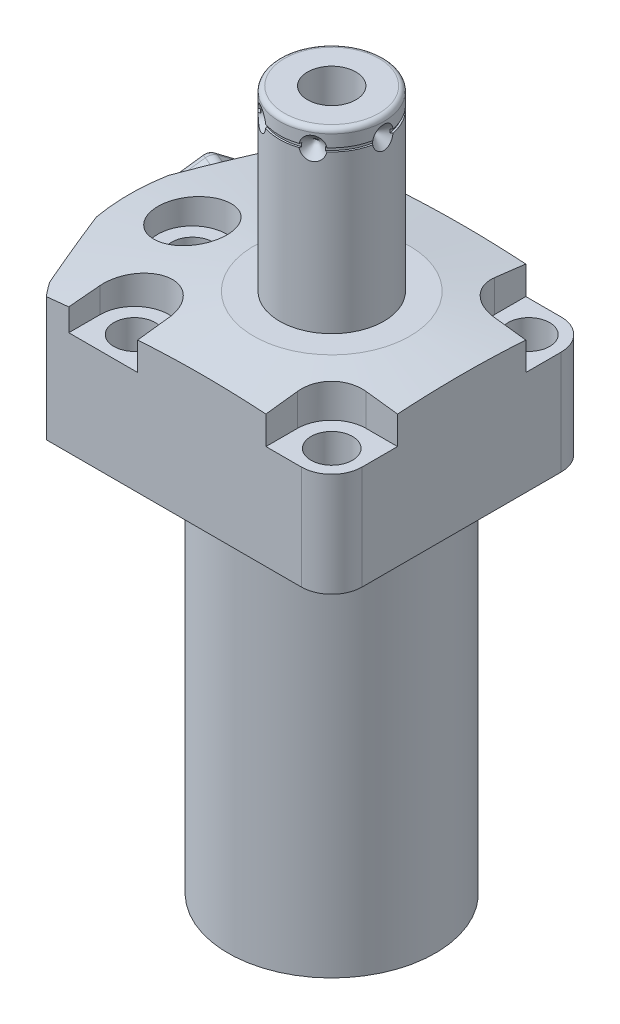
SolidWorks part; units mm, degrees
material "Alloy Steel"
ref_plane "Front Plane" through (0, 0, 0) normal (0, 0, 1) x (1, 0, 0)
ref_plane "Top Plane" through (0, 0, 0) normal (0, 1, 0) x (1, 0, 0)
ref_plane "Right Plane" through (0, 0, 0) normal (1, 0, 0) x (0, 0, -1)
sketch "S2D0002" plane through (0, 0, 0) normal (0, 0, 1) x (1, 0, 0)
  line L0 (-43.18, 0) -> (-43.18, 30.1498)
  line L1 (-43.18, 30.1498) -> (0, 30.1498)
  line L2 (0, 30.1498) -> (0, -80.9752)
  line L3 (0, -80.9752) -> (-22.098, -80.9752)
  line L4 (-22.098, -80.9752) -> (-22.098, 0)
  line L5 (-22.098, 0) -> (-43.18, 0)
  line L6 (0, -3.4925) -> (0, 73.3425) construction
  dimension "D1" = 111.125
  dimension "D2" = 44.196
  dimension "D3" = 86.36
  dimension "D4" = 80.9752
revolve "Revolve1" add sketch "S2D0002" angle 360 about L6
sketch "S2D0001" plane through (0, 0, 0) normal (0, -1, 0) x (1, 0, 0)
  line L0 (-33.136, -27.686) -> (33.136, -27.686)
  line L2 (33.136, 27.686) -> (-33.136, 27.686)
  line L3 (0, 0) -> (59.5614, 0) construction
  arc A0 (-33.136, -27.686) -> (33.136, -27.686) centre (0, 0) ccw
  circle A1 centre (0, 0) radius 43.18
  arc A2 (33.136, 27.686) -> (-33.136, 27.686) centre (0, 0) ccw
  point P4 (25.1041, 0)
  dimension "D1" = 55.372
  dimension "D2" = 0
extrude "Cut-Extrude1" cut sketch "S2D0001" against normal blind 32.9946
sketch "Sketch3" plane through (0, 30.1498, 0) normal (0, -1, 0) x (-1, 0, 0)
  line L0 (21.3317, 58.747) -> (45.6655, 0)
  line L1 (45.6655, 0) -> (21.3317, -58.747)
  line L2 (-32.7616, -13.5703) -> (61.25, 25.3706) construction
  line L3 (0, 0) -> (47.9453, 0) construction
  arc A0 (21.3317, -58.747) -> (21.3317, 58.747) centre (0, 0) ccw
  dimension "D3" = 125
  dimension "D1" = 22.5
  dimension "D2" = 42.1894
extrude "Cut-Extrude2" cut sketch "Sketch3" along normal up to surface (30.1498 mm away) up to face at (0, 0, -22.098)
sketch "Sketch4" plane through (0, 0, 0) normal (0, -1, 0) x (1, 0, 0)
  line L0 (27.686, -33.136) -> (27.686, 33.136)
  line L1 (-33.136, 27.686) -> (33.136, 27.686) construction
  arc A0 (27.686, -33.136) -> (27.686, 33.136) centre (0, 0) ccw
  arc A1 (33.136, -27.686) -> (33.136, 27.686) centre (0, 0) ccw construction
  dimension "D1" = 27.686
extrude "Cut-Extrude3" cut sketch "Sketch4" against normal blind 32.9946
fillet "Fillet1" radius 6.477 2 edges at (27.686, 15.0749, 27.686) (27.686, 15.0749, -27.686)
sketch "Sketch5" plane through (0, 30.1498, 0) normal (0, 1, 0) x (-1, 0, 0)
  line L0 (0, 0) -> (-37.3124, 0) construction
  line L1 (-27.686, 21.209) -> (-27.686, -21.209) construction
  line L2 (-21.209, -27.686) -> (33.136, -27.686) construction
  line L3 (-27.686, -13.6652) -> (-27.686, -27.686)
  line L4 (-27.686, -27.686) -> (-13.6652, -27.686)
  line L5 (-27.686, -13.6652) -> (-21.0058, -13.6652)
  line L6 (-13.6652, -21.0058) -> (-13.6652, -27.686)
  line L7 (-13.6652, 21.0058) -> (-13.6652, 27.686)
  line L8 (-27.686, 13.6652) -> (-21.0058, 13.6652)
  line L9 (0, 0.7832) -> (0, 0) construction
  line L10 (0, 0) -> (47.8281, 0) construction
  line L11 (-27.686, 27.686) -> (-13.6652, 27.686)
  line L12 (-27.686, 13.6652) -> (-27.686, 27.686)
  line L13 (0, 0) -> (0, 43.3168) construction
  line L14 (33.136, 27.686) -> (-21.209, 27.686) construction
  line L15 (13.6652, 27.686) -> (28.3464, 27.686)
  line L16 (13.6652, 27.686) -> (13.6652, 21.0058)
  line L17 (13.6652, -27.686) -> (13.6652, -21.0058)
  line L18 (28.3464, 27.686) -> (28.3464, 21.0058)
  line L19 (28.3464, -27.686) -> (28.3464, -21.0058)
  line L20 (13.6652, -27.686) -> (28.3464, -27.686)
  arc A0 (-13.6652, -21.0058) -> (-21.0058, -13.6652) centre (-21.0058, -21.0058) ccw
  arc A1 (-13.6652, 21.0058) -> (-21.0058, 13.6652) centre (-21.0058, 21.0058) cw
  arc A2 (28.3464, 21.0058) -> (13.6652, 21.0058) centre (21.0058, 21.0058) cw
  arc A3 (28.3464, -21.0058) -> (13.6652, -21.0058) centre (21.0058, -21.0058) ccw
  dimension "D3" = 21.0058
  dimension "D1" = 7.3406
  dimension "D2" = 21.0058
  dimension "D4" = 21.0058
extrude "Cut-Extrude4" cut sketch "Sketch5" against normal blind 8.001
sketch "S2D0003" plane through (0, 0, 0) normal (0, 0, 1) x (1, 0, 0)
  line L0 (-16.637, 30.1498) -> (-86.637, 20.3119)
  line L1 (0, 12.958) -> (0, 26.6311) construction
  line L2 (-16.637, 30.1498) -> (-86.637, 30.1498)
  line L3 (-86.637, 30.1498) -> (-86.637, 20.3119)
  line L4 (-33.136, 30.1498) -> (-28.3464, 30.1498) construction
  dimension "D1" = 33.274
  dimension "D2" = 8
  dimension "D3" = 70
revolve "Cut-Revolve1" cut sketch "S2D0003" angle 360 about L1
ref_plane "Plane20" through (0, 14.5034, 0) normal (0, -1, 0) x (1, 0, 0)
sketch "Sketch7" plane through (0, 14.5034, 0) normal (0, -1, 0) x (1, 0, 0)
  line L0 (-41.1733, -10.1813) -> (-42.8571, -6.1163)
  line L1 (-41.1733, -10.1813) -> (-41.0456, -10.1577)
  line L2 (-41.0456, -10.1577) -> (-40.5499, -10.363)
  line L3 (-40.5499, -10.363) -> (-27.9234, -5.133)
  line L4 (-27.9234, -5.133) -> (-25.6489, -10.6241)
  line L5 (-25.6489, -10.6241) -> (-38.9779, -16.1452)
  line L6 (0, 0) -> (22.0051, 9.1148) construction
  line L7 (-42.4971, -7.6492) -> (-35.4588, -24.6412) construction
  line L8 (-42.8571, -6.1163) -> (-43.0918, -6.2135)
  line L9 (-43.0918, -6.2135) -> (-38.9779, -16.1452)
  line L11 (-42.4971, -7.6492) -> (-35.4588, -24.6412) construction
  dimension "D1" = 14.1732
  dimension "D2" = 11.8872
  dimension "D3" = 45
  dimension "D4" = 0.254
  dimension "D5" = 0.5064
  dimension "D6" = 12.7
  dimension "D7" = 21.5
  dimension "D8" = 78
revolve "Cut-Revolve2" cut sketch "Sketch7" angle 360 about L6
ref_plane "Plane21" through (0, 0, -11.8364) normal (0, 0, 1) x (1, 0, 0)
sketch "Sketch9" plane through (0, 0, -11.8364) normal (0, 0, 1) x (1, 0, 0)
  line L0 (-31.8262, 1.5) -> (-33.575, 1.5)
  line L1 (-31.8262, 1.5) -> (-31.8262, 4.4972)
  line L2 (-31.8262, 4.4972) -> (-29.8196, 4.4972)
  line L3 (-29.8196, 4.4972) -> (-29.8196, 12.0664)
  line L4 (-29.8196, 12.0664) -> (-28.575, 12.0664)
  line L5 (-28.575, 12.0664) -> (-28.575, 0)
  line L6 (-28.575, -17.8934) -> (-28.575, 0.5283) construction
  line L7 (-33.136, 0) -> (21.209, 0) construction
  line L8 (-33.575, 0) -> (-33.575, 1.5)
  line L9 (-35.4588, 0) -> (-42.4971, 0) construction
  line L10 (-33.575, 0) -> (-28.575, 0)
  dimension "D1" = 7.5692
  dimension "D2" = 2.9972
  dimension "D3" = 28.575
  dimension "D4" = 2.4892
  dimension "D5" = 6.5024
  dimension "D6" = 10
  dimension "D7" = 1.5
revolve "Cut-Revolve4" cut sketch "Sketch9" angle 360 about L6
sketch "Sketch11" plane through (0, 4.4972, 0) normal (0, -1, 0) x (1, 0, 0)
  circle A0 centre (-28.575, -11.8364) radius 2.7432
  circle A1 centre (-28.575, -11.8364) radius 3.2512 construction
  dimension "D1" = 5.4864
extrude "Extrude1" add sketch "Sketch11" along normal blind 2.9972
sketch "Sketch12" plane through (0, 1.5, 0) normal (0, -1, 0) x (1, 0, 0)
  line L7 (-27.3304, -12.555) -> (-27.3304, -11.1178)
  line L8 (-27.3304, -11.1178) -> (-28.575, -10.3993)
  line L9 (-28.575, -10.3993) -> (-29.8196, -11.1178)
  line L10 (-29.8196, -11.1178) -> (-29.8196, -12.555)
  line L11 (-29.8196, -12.555) -> (-28.575, -13.2735)
  line L12 (-28.575, -13.2735) -> (-27.3304, -12.555)
  circle A0 centre (-28.575, -11.8364) radius 1.2446 construction
  circle A1 centre (-28.575, -11.8364) radius 2.7432 construction
  dimension "D2" = 2.4892
extrude "Cut-Extrude5" cut sketch "Sketch12" against normal blind 1.27
chamfer "Chamfer1" distance 0.254 angle 45 1 edges at (-28.575, 1.5, -14.5796)
mirror "Mirror2" about plane through (0, 0, 0) normal (0, 0, 1) of "Chamfer1", "Cut-Extrude5", "Extrude1", "Cut-Revolve4", "Cut-Revolve2"
sketch "Sketch16" plane through (-18.1864, 0, -11.8364) normal (0, 0, -1) x (-1, 0, 0)
  line L0 (10.3886, -0.4101) -> (10.3886, 1.5457) construction
  line L1 (5.3886, 1.5) -> (15.3886, 1.5) construction
  line L2 (7.1374, 4.4972) -> (7.1374, 1.5) construction
  line L3 (13.6398, 1.5) -> (13.6398, 4.4972) construction
  circle A0 centre (14.3886, 0.5) radius 1
  dimension "D2" = 2
  dimension "D1" = 8
  dimension "D3" = 1
revolve "Revolve3" add sketch "Sketch16" angle 360 about L0
mirror "Mirror3" about plane through (0, 0, 0) normal (0, 0, 1) of bodies 123 141
sketch "Sketch17" plane through (0, 0, 0) normal (1, 0, 0) x (0, 0, -1)
  line L0 (0, 30.1498) -> (-11.1125, 30.1498)
  line L1 (-11.1125, 30.1498) -> (-11.1125, 67.018)
  line L2 (-10.0965, 68.034) -> (0, 68.034)
  line L3 (0, 68.034) -> (0, 30.1498)
  line L4 (0, 24.9961) -> (0, 47.2925) construction
  line L5 (16.637, 30.1498) -> (-16.637, 30.1498) construction
  line L6 (-24.6412, 0) -> (-7.6492, 0) construction
  arc A0 (-10.0965, 68.034) -> (-11.1125, 67.018) centre (-10.0965, 67.018) ccw
  dimension "D2" = 1.016
  dimension "D1" = 22.225
  dimension "D3" = 68.034
revolve "Revolve4" add sketch "Sketch17" angle 360 about L4
sketch "Sketch18" plane through (0, 0, 0) normal (0, 0, 1) x (1, 0, 0)
  line L0 (5.1562, 68.034) -> (5.1562, 51.016)
  line L1 (5.1562, 51.016) -> (0, 47.9178)
  line L2 (5.1562, 68.034) -> (0, 68.034)
  line L3 (0, 68.034) -> (0, 47.9178)
  line L4 (0, -20.476) -> (0, 0.5839) construction
  line L5 (10.0965, 68.034) -> (-10.0965, 68.034) construction
  dimension "D1" = 17.018
  dimension "D2" = 10.3124
  dimension "D3" = 59
revolve "Cut-Revolve7" cut sketch "Sketch18" angle 360 about L4
sketch "Sketch19" plane through (-52.2568, 0, 16.5766) normal (-0.9239, 0, -0.3827) x (-0.3827, 0, 0.9239)
  circle A0 centre (-35.3126, 14.5034) radius 8.5
  circle A1 centre (-35.3126, 14.5034) radius 5.9436 construction
  dimension "D1" = 17
extrude "Extrude3" add sketch "Sketch19" along normal blind 1
sketch "Sketch20" plane through (0, 0, 0) normal (0, 0, 1) x (1, 0, 0)
  line L3 (0, 64.0716) -> (4.3349, 64.0716) construction
  line L4 (-11.1125, 67.018) -> (-11.1125, 30.1498) construction
  line L5 (10.0965, 68.034) -> (-10.0965, 68.034) construction
  line L6 (-11.1125, 61.6586) -> (-11.1125, 64.0716)
  line L7 (-11.1125, 64.0716) -> (-8.6995, 64.0716)
  line L8 (-8.6995, 64.0716) -> (-11.1125, 61.6586)
  dimension "D1" = 3.9624
  dimension "D2" = 4.826
  dimension "D4" = 45
revolve "Cut-Revolve8" cut sketch "Sketch20" angle 360 about L3
sketch "Sketch22" plane through (0, 0, 0) normal (1, 0, 0) x (0, 0, -1)
  line L0 (11.1125, 64.453) -> (10.7315, 64.453)
  line L1 (10.7315, 64.453) -> (10.7315, 63.691)
  line L2 (10.7315, 63.691) -> (11.1125, 63.691)
  line L3 (11.1125, 63.691) -> (11.1125, 64.453)
  line L4 (0, 41.8979) -> (0, 49.0468) construction
  line L5 (5.1562, 68.034) -> (-5.1562, 68.034) construction
  line L6 (10.0965, 68.034) -> (-10.0965, 68.034) construction
  line L7 (11.1125, 30.1498) -> (11.1125, 67.018) construction
  dimension "D1" = 0.762
  dimension "D2" = 0.381
  dimension "D3" = 3.581
revolve "Cut-Revolve6" cut sketch "Sketch22" angle 360 about L4
hole_wizard "Hole1" positions "Sketch24" profile "Sketch23" legacy end condition up to next
sketch "Sketch24" plane through (0, 30.1498, 0) normal (0, 1, 0) x (-1, 0, 0)
  arc A0 (-13.6652, -21.0058) -> (-21.0058, -13.6652) centre (-21.0058, -21.0058) ccw construction
  arc A1 (-21.0058, 13.6652) -> (-13.6652, 21.0058) centre (-21.0058, 21.0058) ccw construction
  point P0 (29.6926, 0)
  point P1 (-21.0058, 21.0058)
  point P3 (-21.0058, -21.0058)
  point P15 (21.0058, 21.0058)
  point P18 (21.0058, -21.0058)
  dimension "D1" = 29.6926
sketch "Sketch23" plane through (-29.6926, 30.1498, 0) normal (1, 0, 0) x (0, 0, 1)
  line L0 (0, 0) -> (0, 30.1498)
  line L1 (0, 30.1498) -> (4.4196, 30.1498)
  line L2 (4.4196, 30.1498) -> (4.4196, 8.001)
  line L3 (4.4196, 8.001) -> (7.3406, 8.001)
  line L4 (7.3406, 8.001) -> (7.3406, 0)
  line L5 (7.3406, 0) -> (0, 0)
  line L6 (0, 110) -> (0, -10) construction
  dimension "Diameter" = 8.8392
  dimension "Depth" = 30.1498
  dimension "C-Bore Diameter" = 14.6812
  dimension "C-Bore Depth" = 8.001
sketch "Sketch25" plane through (0, -80.9752, 0) normal (0, -1, 0) x (1, 0, 0)
  circle A0 centre (0, 0) radius 11.3665
  dimension "D1" = 22.733
extrude "Cut-Extrude7" cut sketch "Sketch25" against normal blind 1.524
sketch "Sketch27" plane through (-39.6671, 0, -16.4307) normal (-0.9239, 0, -0.3827) x (-0.3827, 0, 0.9239)
  line L1 (8.3998, 19.5804) -> (-0.1969, 24.3164)
  line L2 (-0.1969, 24.3164) -> (-8.5967, 19.2394)
  line L3 (-8.5967, 19.2394) -> (-8.3998, 9.4264)
  line L4 (-8.3998, 9.4264) -> (0.1969, 4.6904)
  line L5 (0.1969, 4.6904) -> (8.5967, 9.7674)
  line L6 (8.5967, 9.7674) -> (8.3998, 19.5804)
  circle A0 centre (0, 14.5034) radius 8.5 construction
  dimension "D1" = 17
extrude "Extrude4" add sketch "Sketch27" along normal blind 6.87
fillet "Fillet2" radius 2 12 edges at (-39.5508, 19.2394, -25.6875) (-42.762, 14.3329, -26.9111) (-44.4446, 7.0584, -22.849) (-39.6262, 9.4264, -25.5056) (-42.916, 4.6904, -17.5633) (-47.6968, 7.2289, -14.9976) (-46.1305, 9.7674, -9.8028) (-46.0551, 19.5804, -9.9848) (-49.2663, 14.6739, -11.2083) (-47.5837, 21.9484, -15.2705) (-42.7653, 24.3164, -17.9271) (-44.3316, 21.7779, -23.1218)
pattern_circular "CirPattern1" count 6 over 360 about axis through (0, -3.4925, 0) along (0, 1, 0) of "Cut-Revolve8"
